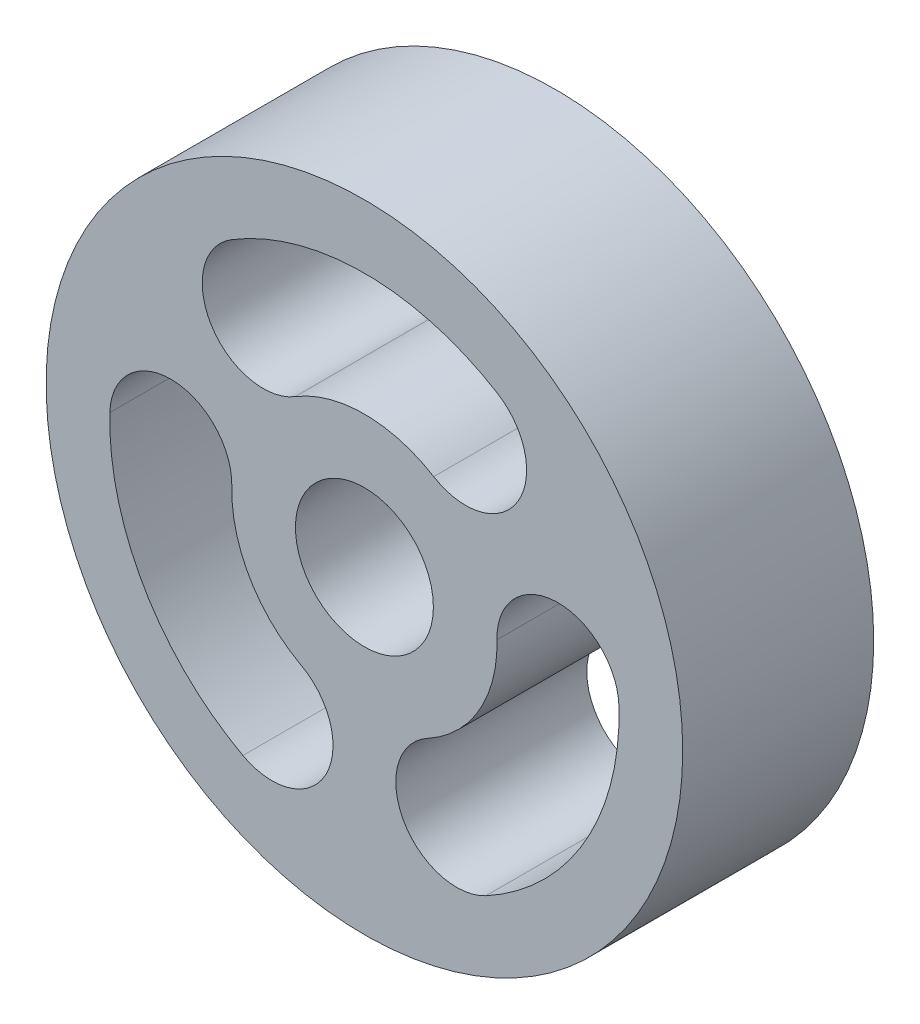
SolidWorks part; units mm, degrees
ref_plane "前视基准面" through (0, 0, 0) normal (0, 0, 1) x (1, 0, 0)
ref_plane "上视基准面" through (0, 0, 0) normal (0, 1, 0) x (1, 0, 0)
ref_plane "右视基准面" through (0, 0, 0) normal (1, 0, 0) x (0, 0, -1)
other "Configuration Table"
sketch "草图1" plane through (0, 0, 0) normal (0, 0, 1) x (1, 0, 0)
  line L0 (0, 3.25) -> (0, 9.125) construction
  line L1 (0, 9.125) -> (0, 15) construction
  line L2 (-4.7678, 7.7803) -> (0, 0) construction
  line L3 (0, 0) -> (4.7678, 7.7803) construction
  circle A0 centre (0, 0) radius 3.25
  circle A1 centre (0, 0) radius 15
  circle A2 centre (0, 0) radius 9.125 construction
  arc A3 (-4.7678, 7.7803) -> (4.7678, 7.7803) centre (0, 0) cw construction
  arc A4 (6.27, 10.2317) -> (-6.27, 10.2317) centre (0, 0) ccw
  arc A5 (3.2656, 5.329) -> (-3.2656, 5.329) centre (0, 0) ccw
  arc A6 (3.2656, 5.329) -> (6.27, 10.2317) centre (4.7678, 7.7803) ccw
  arc A7 (-6.27, 10.2317) -> (-3.2656, 5.329) centre (-4.7678, 7.7803) ccw
  arc A8 (9.1219, 0.2389) -> (4.3541, -8.0192) centre (0, 0) cw construction
  arc A9 (5.7259, -10.5458) -> (11.9959, 0.3141) centre (0, 0) ccw
  arc A10 (2.9822, -5.4926) -> (6.2479, 0.1636) centre (0, 0) ccw
  arc A11 (2.9822, -5.4926) -> (5.7259, -10.5458) centre (4.3541, -8.0192) ccw
  arc A12 (11.9959, 0.3141) -> (6.2479, 0.1636) centre (9.1219, 0.2389) ccw
  arc A13 (-4.3541, -8.0192) -> (-9.1219, 0.2389) centre (0, 0) cw construction
  arc A14 (-11.9959, 0.3141) -> (-5.7259, -10.5458) centre (0, 0) ccw
  arc A15 (-6.2479, 0.1636) -> (-2.9822, -5.4926) centre (0, 0) ccw
  arc A16 (-6.2479, 0.1636) -> (-11.9959, 0.3141) centre (-9.1219, 0.2389) ccw
  arc A17 (-5.7259, -10.5458) -> (-2.9822, -5.4926) centre (-4.3541, -8.0192) ccw
  point P10 (0, 9.125)
  point P18 (0, 9.125)
  point P23 (7.9025, -4.5625)
  point P30 (-7.9025, -4.5625)
  point P35 (0, 0)
  dimension "D1" = 30
  dimension "D2" = 6.5
  dimension "D4" = 3
  dimension "D5" = 63
  dimension "D3" = 3
extrude "凸台-拉伸1" add sketch "草图1" along normal blind 9
